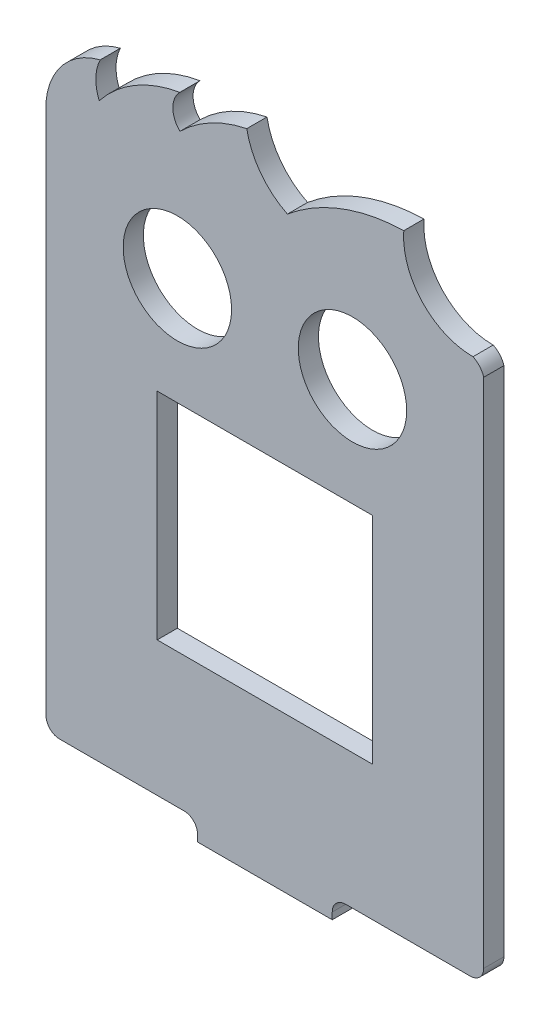
SolidWorks part; units mm, degrees
ref_plane "Alzado" through (0, 0, 0) normal (0, 0, 1) x (1, 0, 0)
ref_plane "Planta" through (0, 0, 0) normal (0, 1, 0) x (1, 0, 0)
ref_plane "Vista lateral" through (0, 0, 0) normal (1, 0, 0) x (0, 0, -1)
sketch "Model" plane through (0, 0, 0) normal (0, 0, 1) x (1, 0, 0)
  line L0 (74.699, -33.021) -> (74.699, -1.021)
  line L1 (74.699, -1.021) -> (42.699, -1.021)
  line L2 (42.699, -1.021) -> (42.699, -33.021)
  line L3 (42.699, -33.021) -> (74.699, -33.021)
  line L4 (58.699, -1.021) -> (58.699, -74.8274) construction
  line L5 (48.699, -56.021) -> (68.699, -56.021) construction
  line L6 (89.199, -53.021) -> (70.699, -53.021)
  line L7 (28.199, -53.021) -> (46.699, -53.021)
  line L8 (48.699, -56.021) -> (68.699, -56.021)
  line L49 (48.699, -56.021) -> (48.699, -55.021)
  line L51 (26.199, 28.0052) -> (26.199, -51.021)
  line L52 (91.199, -51.021) -> (91.199, 25.0041)
  line L54 (68.699, -55.021) -> (68.699, -56.021)
  circle A0 centre (71.699, 14.979) radius 8.05
  circle A1 centre (45.699, 14.979) radius 8.05
  arc A2 (48.699, -55.021) -> (46.699, -53.021) centre (46.699, -55.021) ccw
  arc A3 (70.699, -53.021) -> (68.699, -55.021) centre (70.699, -55.021) ccw
  arc A32 (26.199, -51.021) -> (28.199, -53.021) centre (28.199, -51.021) ccw
  arc A33 (34.2352, 37.3439) -> (26.199, 28.0052) centre (36.7972, 27.0122) ccw
  arc A34 (34.2352, 37.3439) -> (34.0881, 32.0212) centre (40.1102, 34.5183) ccw
  arc A35 (46.0557, 39.0765) -> (34.0881, 32.0212) centre (49.2438, 19.991) ccw
  arc A36 (46.0557, 39.0765) -> (46.0788, 34.0765) centre (48.5672, 36.588) ccw
  arc A37 (56.0043, 39.3865) -> (46.0788, 34.0765) centre (59.9969, 19.9918) ccw
  arc A38 (56.0043, 39.3865) -> (62.0412, 31.4142) centre (66.995, 41.4371) ccw
  arc A39 (79.3217, 37.922) -> (62.0412, 31.4142) centre (79.9719, 9.9986) ccw
  arc A40 (79.3217, 37.922) -> (89.6011, 26.8493) centre (89.6011, 37.1571) ccw
  arc A41 (91.199, 25.0041) -> (89.6011, 26.8493) centre (88.3283, 24.1327) ccw
  arc A42 (89.199, -53.021) -> (91.199, -51.021) centre (89.199, -51.021) ccw
  point P11 (68.699, -53.021)
  dimension "D5" = 2
  dimension "D1" = 10
  dimension "D2" = 13
  dimension "D3" = 10
  dimension "D4" = 3
extrude "Saliente-Extruir1" add sketch "Model" against normal blind 3
sketch "Croquis2" plane through (0, 0, -3) normal (0, 0, -1) x (-1, 0, 0)
  line L0 (-68.699, -56.021) -> (-68.699, -52.6526)
  line L1 (-68.699, -52.6526) -> (-48.699, -52.6526)
  line L2 (-48.699, -52.6526) -> (-48.699, -56.021)
  line L3 (-48.699, -56.021) -> (-68.699, -56.021) construction
  line L4 (-68.699, -56.021) -> (-48.699, -56.021)
extrude "Saliente-Extruir2" add sketch "Croquis2" along normal blind 8
sketch "Croquis3" plane through (0, -52.6526, 0) normal (0, 1, 0) x (1, 0, 0)
  line L0 (58.699, 11) -> (58.699, 3) construction
  line L1 (48.699, 11) -> (68.699, 11) construction
  line L2 (48.699, 3) -> (68.699, 3) construction
  circle A0 centre (64.699, 6.5) radius 1.5
  circle A1 centre (52.699, 6.5) radius 1.5
  dimension "D1" = 6
  dimension "D2" = 3.5
extrude "Cortar-Extruir1" cut sketch "Croquis3" against normal blind 4
fillet "Redondeo1" radius 2 2 edges at (48.699, -54.3368, -11) (68.699, -54.3368, -11)
sketch "Croquis4" plane through (0, -52.6526, 0) normal (0, 1, 0) x (1, 0, 0)
  circle A0 centre (52.699, 6.5) radius 2.25
  circle A1 centre (64.699, 6.5) radius 2.25
extrude "Cortar-Extruir2" cut sketch "Croquis4" against normal blind 1
